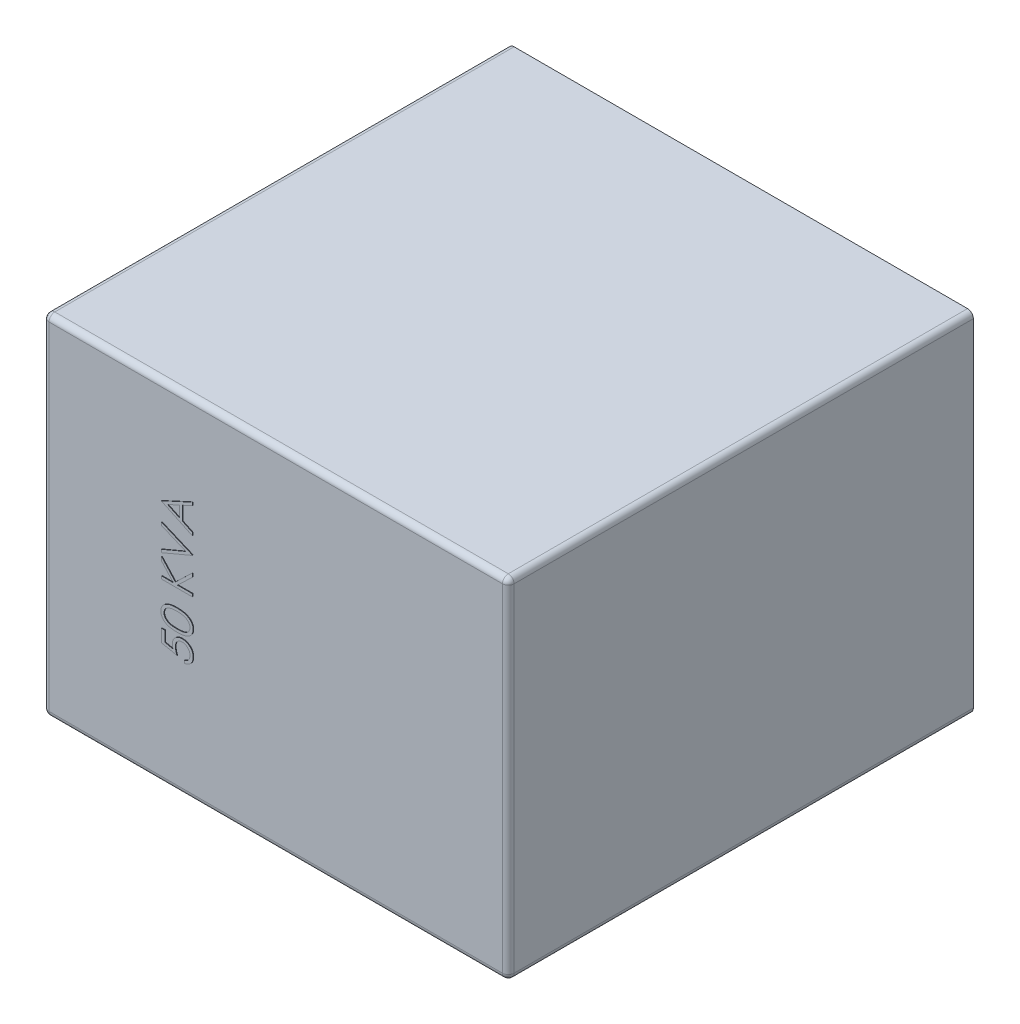
SolidWorks part; units mm, degrees
ref_plane "Alzado" through (0, 0, 0) normal (0, 0, 1) x (1, 0, 0)
ref_plane "Planta" through (0, 0, 0) normal (0, 1, 0) x (1, 0, 0)
ref_plane "Vista lateral" through (0, 0, 0) normal (1, 0, 0) x (0, 0, -1)
sketch "Croquis1" plane through (0, 0, 0) normal (0, 0, 1) x (1, 0, 0)
  line L1 (-400, -300) -> (400, -300)
  line L2 (-400, -300) -> (-400, 300)
  line L3 (-400, 300) -> (400, 300)
  line L4 (400, -300) -> (400, 300)
  line L5 (-400, -300) -> (400, 300) construction
  line L6 (-400, 300) -> (400, -300) construction
  point P0 (0, 0)
  dimension "D1" = 800
  dimension "D2" = 600
extrude "Saliente-Extruir1" add sketch "Croquis1" along normal blind 800
sketch "Croquis2" plane through (0, 0, 800) normal (0, 0, 1) x (1, 0, 0)
  line L0 (-142.4086, -225.8313) -> (-142.4086, 220.7754) construction
  text T0 "      50 KVA" font "Century Gothic" height in points 200
extrude "Saliente-Extruir2" add sketch "Croquis2" along normal blind 1
fillet "Redondeo1" radius 10 8 edges at (0, 300, 800) (-400, 300, 400) (-400, 0, 800) (-400, -300, 400) (0, -300, 800) (400, -300, 400) (400, 300, 400) (400, 0, 800)
sketch "Croquis3" plane through (-400, 0, 0) normal (-1, 0, 0) x (0, 0, 1)
  line L1 (463.7781, 183.9283) -> (679.7672, 183.9283)
  line L2 (463.7781, 183.9283) -> (463.7781, -183.9283)
  line L3 (463.7781, -183.9283) -> (679.7672, -183.9283)
  line L4 (679.7672, 183.9283) -> (679.7672, -183.9283)
  line L5 (463.7781, 183.9283) -> (679.7672, -183.9283) construction
  line L6 (463.7781, -183.9283) -> (679.7672, 183.9283) construction
  line L7 (465.7144, 180.6305) -> (677.8309, 180.6305)
  line L8 (465.7144, 180.6305) -> (465.7144, -180.6305)
  line L9 (465.7144, -180.6305) -> (677.8309, -180.6305)
  line L10 (677.8309, 180.6305) -> (677.8309, -180.6305)
  line L11 (465.7144, 180.6305) -> (677.8309, -180.6305) construction
  line L12 (465.7144, -180.6305) -> (677.8309, 180.6305) construction
  point P0 (571.7726, 0)
  point P5 (571.7726, 0)
extrude "Saliente-Extruir3" add sketch "Croquis3" along normal blind 100
sketch "Croquis4" plane through (-400, 0, 0) normal (-1, 0, 0) x (0, 0, 1)
  line L1 (544.2415, 123.1887) -> (599.3037, 123.1887)
  line L2 (544.2415, 123.1887) -> (544.2415, 133.8236)
  line L3 (544.2415, 133.8236) -> (599.3037, 133.8236)
  line L4 (599.3037, 123.1887) -> (599.3037, 133.8236)
  line L5 (544.2415, 123.1887) -> (599.3037, 133.8236) construction
  line L6 (544.2415, 133.8236) -> (599.3037, 123.1887) construction
  line L7 (544.2415, 59.3795) -> (599.3037, 59.3795)
  line L8 (544.2415, 59.3795) -> (544.2415, 50.074)
  line L9 (544.2415, 50.074) -> (599.3037, 50.074)
  line L10 (599.3037, 59.3795) -> (599.3037, 50.074)
  line L11 (544.2415, 59.3795) -> (599.3037, 50.074) construction
  line L12 (544.2415, 50.074) -> (599.3037, 59.3795) construction
  line L13 (544.2415, -62.2569) -> (599.3037, -62.2569)
  line L14 (544.2415, -62.2569) -> (544.2415, -51.622)
  line L15 (544.2415, -51.622) -> (599.3037, -51.622)
  line L16 (599.3037, -62.2569) -> (599.3037, -51.622)
  line L17 (544.2415, -62.2569) -> (599.3037, -51.622) construction
  line L18 (544.2415, -51.622) -> (599.3037, -62.2569) construction
  line L19 (544.2415, -133.3776) -> (599.3037, -133.3776)
  line L20 (544.2415, -133.3776) -> (544.2415, -124.0721)
  line L21 (544.2415, -124.0721) -> (599.3037, -124.0721)
  line L22 (599.3037, -133.3776) -> (599.3037, -124.0721)
  line L23 (544.2415, -133.3776) -> (599.3037, -124.0721) construction
  line L24 (544.2415, -124.0721) -> (599.3037, -133.3776) construction
  point P0 (571.7726, 128.5062)
  point P5 (571.7726, 54.7267)
  point P10 (571.7726, -56.9395)
  point P15 (571.7726, -128.7249)
extrude "Saliente-Extruir4" add sketch "Croquis4" along normal blind 100
